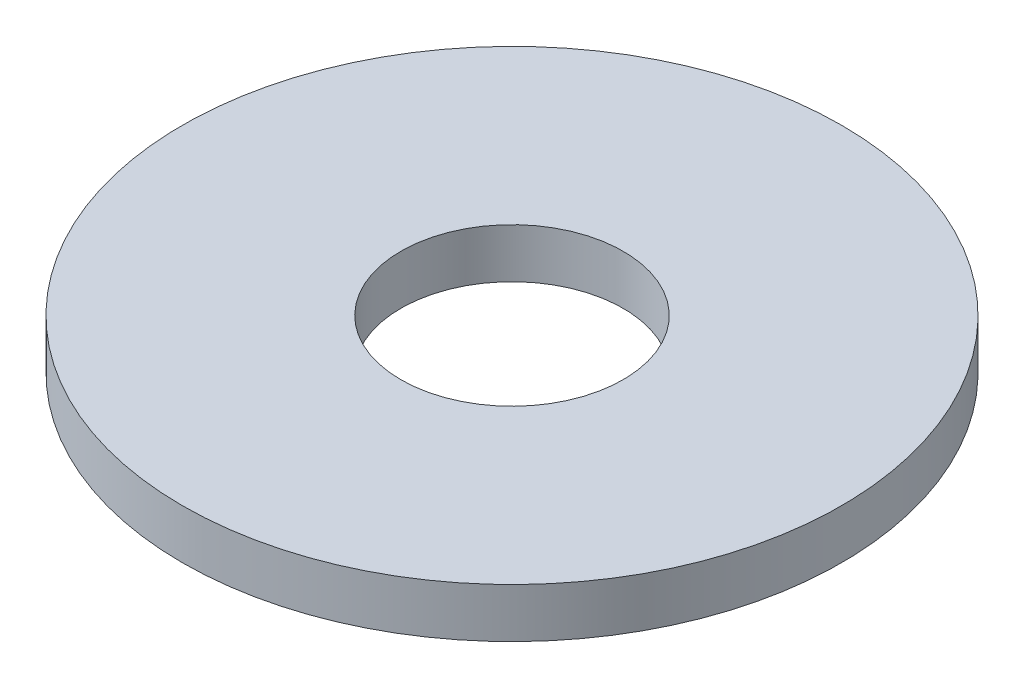
SolidWorks part; units mm, degrees
material "Plain Carbon Steel"
ref_plane "Front" through (0, 0, 0) normal (0, 0, 1) x (1, 0, 0)
ref_plane "Top" through (0, 0, 0) normal (0, 1, 0) x (1, 0, 0)
ref_plane "Right" through (0, 0, 0) normal (1, 0, 0) x (0, 0, -1)
sketch "Sketch1" plane through (0, 0, 0) normal (0, 1, 0) x (1, 0, 0)
  circle A0 centre (0, 0) radius 13.5
  circle A1 centre (0, 0) radius 40
  dimension "D1" = 27
  dimension "D2" = 80
extrude "Boss-Extrude1" add sketch "Sketch1" along normal blind 6
